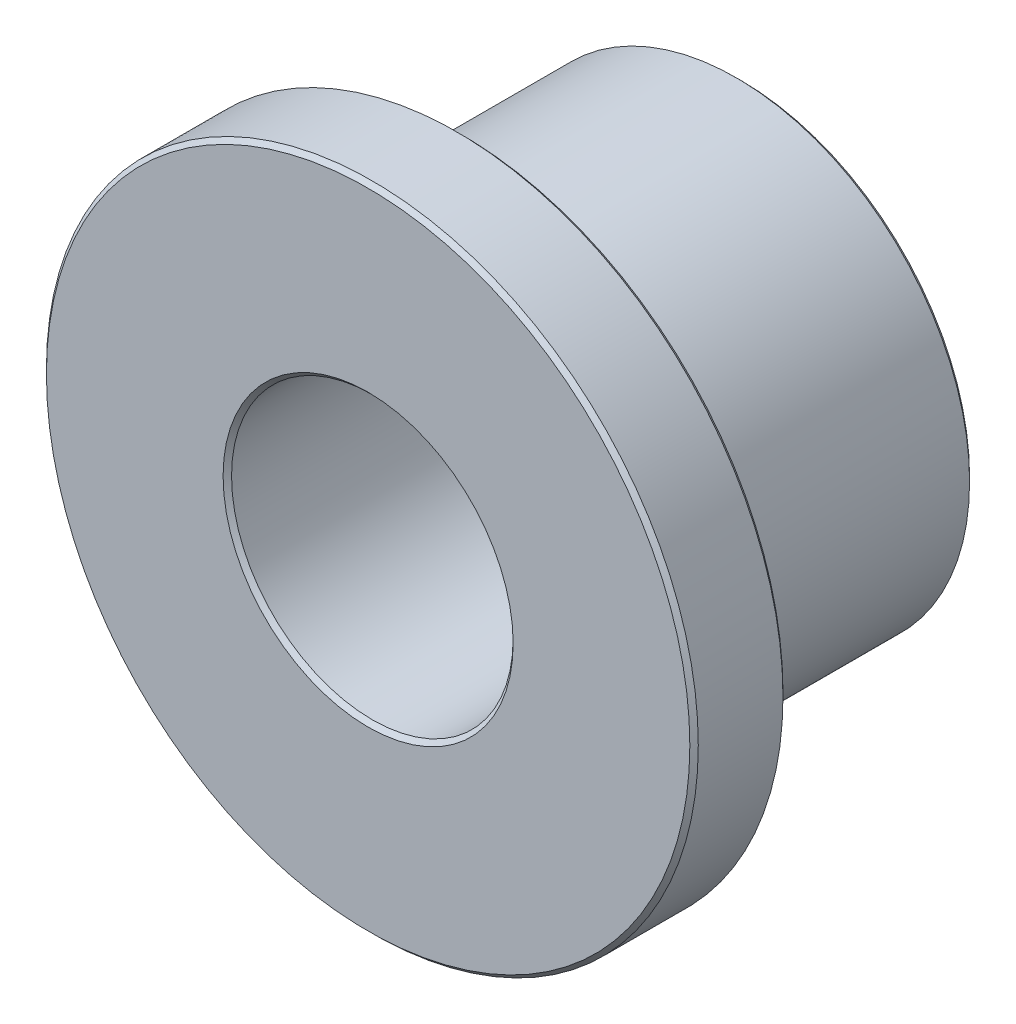
SolidWorks part; units mm, degrees
ref_plane "Front" through (0, 0, 0) normal (0, 0, 1) x (1, 0, 0)
ref_plane "Top" through (0, 0, 0) normal (0, 1, 0) x (1, 0, 0)
ref_plane "Right" through (0, 0, 0) normal (1, 0, 0) x (0, 0, -1)
sketch "Sketch1" plane through (0, 0, 0) normal (0, 0, 1) x (1, 0, 0)
  circle A0 centre (0, 0) radius 2.4003
  circle A1 centre (0, 0) radius 3.9751
  circle A2 centre (0, 0) radius 5.5562
  dimension "ID" = 4.8006
  dimension "OD" = 7.9502
  dimension "Flange OD" = 11.1125
sketch "Sketch2" plane through (0, 0, 0) normal (1, 0, 0) x (0, 0, -1)
  line L0 (-3.175, -5.5562) -> (3.175, -5.5562) construction
  line L1 (0, 5.5562) -> (0, -5.5562) construction
  line L3 (-1.5875, 3.9751) -> (3.175, 3.9751) construction
  point P3 (0, -5.5562)
  point P7 (0, 3.9751)
  point P9 (-1.5875, -5.5563)
  point P10 (-3.175, 5.5563)
  point P23 (0, 5.5562)
  dimension "Flange Thickness" = 1.5875
  dimension "Length" = 6.35
sketch "Sketch3" plane through (0, 0, 0) normal (0, 0, 1) x (1, 0, 0)
  circle A0 centre (0, 0) radius 5.5562 construction
  circle A1 centre (0, 0) radius 5.5562
  circle A2 centre (0, 0) radius 2.4003 construction
  circle A3 centre (0, 0) radius 2.4003
extrude "Boss-Extrude1" add sketch "Sketch3" against normal up to vertex (-1.5875 mm away) from vertex at 3.175 starting at point (0, -5.5562, 3.175)
sketch "Sketch4" plane through (0, 0, 0) normal (0, 0, 1) x (1, 0, 0)
  circle A0 centre (0, 0) radius 2.4003 construction
  circle A1 centre (0, 0) radius 3.9751 construction
  circle A2 centre (0, 0) radius 2.4003
  circle A3 centre (0, 0) radius 3.9751
extrude "Boss-Extrude2" add sketch "Sketch4" against normal up to vertex (3.175 mm away) from vertex at 1.5875 starting at point (0, -5.5563, 1.5875)
chamfer "Chamfer1" distance 0.072 angle 45 6 edges at (2.4003, 0, 3.175) (5.5562, 0, 3.175) (5.5562, 0, 1.5875) (3.9751, 0, 1.5875) (2.4003, 0, -3.175) (3.9751, 0, -3.175)
equation "\"D1@Chamfer1\"=\"ID@Sketch1\"*0.015"
